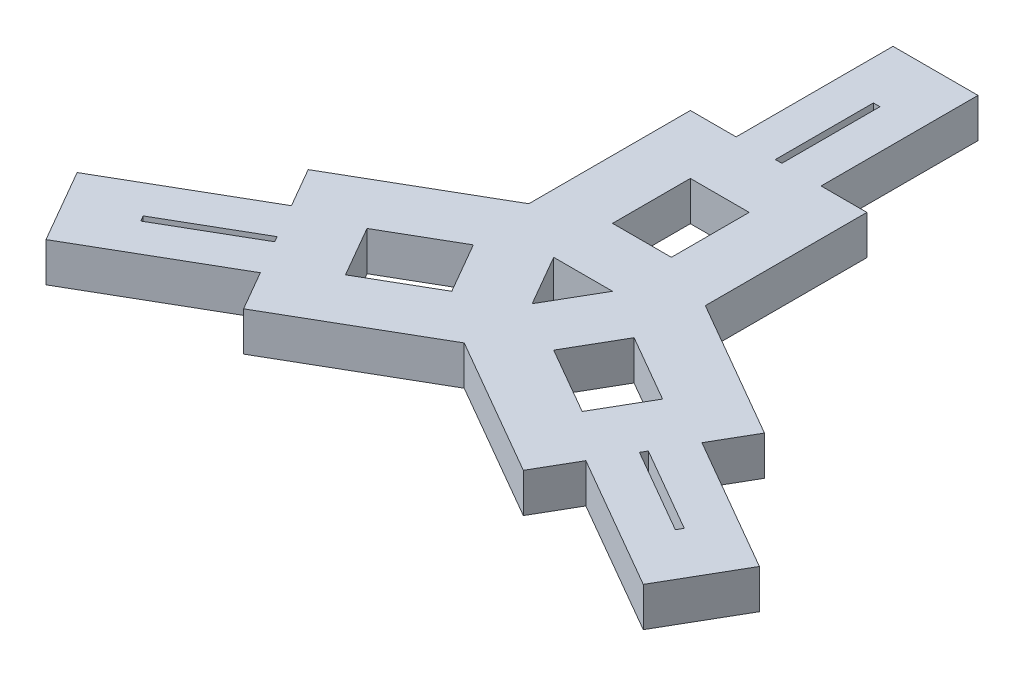
SolidWorks part; units mm, degrees
ref_plane "Alzado" through (0, 0, 0) normal (0, 0, 1) x (1, 0, 0)
ref_plane "Planta" through (0, 0, 0) normal (0, 1, 0) x (1, 0, 0)
ref_plane "Vista lateral" through (0, 0, 0) normal (1, 0, 0) x (0, 0, -1)
sketch "Croquis1" plane through (0, 0, 0) normal (0, 1, 0) x (1, 0, 0)
  line L0 (0, -1000) -> (0, 49000) construction
  line L1 (-1000, 0) -> (49000, 0) construction
  line L7 (-65, 475) -> (-5, 475)
  line L8 (-65, 475) -> (-65, 325)
  line L9 (-65, 325) -> (-5, 325)
  line L10 (-5, 475) -> (-5, 325)
  line L11 (-65, 475) -> (-5, 325) construction
  line L12 (-65, 325) -> (-5, 475) construction
  line L16 (65, 475) -> (5, 325) construction
  line L17 (65, 325) -> (5, 475) construction
  line L18 (65, 325) -> (5, 325)
  line L19 (5, 475) -> (5, 325)
  line L20 (65, 475) -> (5, 475)
  line L21 (65, 475) -> (65, 325)
  line L22 (-135, 235) -> (-135, 77.9423)
  line L23 (-65, 475) -> (65, 475)
  line L24 (-65, 475) -> (-65, 565)
  line L25 (-65, 565) -> (65, 565)
  line L26 (65, 475) -> (65, 565)
  line L35 (-135, 235) -> (135, 235)
  line L36 (-135, 235) -> (-135, 325)
  line L37 (-135, 325) -> (135, 325)
  line L38 (135, 235) -> (135, 325)
  line L39 (-135, 235) -> (135, 325) construction
  line L40 (-135, 325) -> (135, 235) construction
  line L41 (-45, 235) -> (-45, 25.9808)
  line L42 (45, 235) -> (45, 25.9808)
  line L43 (135, 235) -> (135, 77.9423)
  line L44 (378.8621, -293.7917) -> (278.9583, -166.8301) construction
  line L45 (248.9583, -218.7917) -> (408.8621, -241.8301) construction
  line L46 (313.9583, -106.2083) -> (413.8621, -233.1699) construction
  line L47 (443.8621, -181.2083) -> (283.9583, -158.1699) construction
  line L48 (443.8621, -181.2083) -> (313.9583, -106.2083)
  line L49 (443.8621, -181.2083) -> (413.8621, -233.1699)
  line L50 (413.8621, -233.1699) -> (283.9583, -158.1699)
  line L51 (313.9583, -106.2083) -> (283.9583, -158.1699)
  line L52 (248.9583, -218.7917) -> (278.9583, -166.8301)
  line L53 (408.8621, -241.8301) -> (278.9583, -166.8301)
  line L54 (378.8621, -293.7917) -> (408.8621, -241.8301)
  line L55 (378.8621, -293.7917) -> (248.9583, -218.7917)
  line L56 (443.8621, -181.2083) -> (521.8044, -226.2083)
  line L57 (443.8621, -181.2083) -> (378.8621, -293.7917)
  line L58 (378.8621, -293.7917) -> (456.8044, -338.7917)
  line L59 (521.8044, -226.2083) -> (456.8044, -338.7917)
  line L60 (271.016, -0.5866) -> (348.9583, -45.5866)
  line L61 (271.016, -0.5866) -> (136.016, -234.4134)
  line L62 (136.016, -234.4134) -> (213.9583, -279.4134)
  line L63 (348.9583, -45.5866) -> (213.9583, -279.4134)
  line L64 (226.016, -78.5289) -> (45, 25.9808)
  line L65 (271.016, -0.5866) -> (135, 77.9423)
  line L66 (181.016, -156.4711) -> (0, -51.9615)
  line L67 (136.016, -234.4134) -> (0, -155.8846)
  line L68 (-443.8621, -181.2083) -> (-283.9583, -158.1699) construction
  line L69 (-313.9583, -106.2083) -> (-413.8621, -233.1699) construction
  line L70 (-248.9583, -218.7917) -> (-408.8621, -241.8301) construction
  line L71 (-378.8621, -293.7917) -> (-278.9583, -166.8301) construction
  line L72 (-378.8621, -293.7917) -> (-248.9583, -218.7917)
  line L73 (-378.8621, -293.7917) -> (-408.8621, -241.8301)
  line L74 (-408.8621, -241.8301) -> (-278.9583, -166.8301)
  line L75 (-248.9583, -218.7917) -> (-278.9583, -166.8301)
  line L76 (-313.9583, -106.2083) -> (-283.9583, -158.1699)
  line L77 (-413.8621, -233.1699) -> (-283.9583, -158.1699)
  line L78 (-443.8621, -181.2083) -> (-413.8621, -233.1699)
  line L79 (-443.8621, -181.2083) -> (-313.9583, -106.2083)
  line L80 (-378.8621, -293.7917) -> (-456.8044, -338.7917)
  line L81 (-378.8621, -293.7917) -> (-443.8621, -181.2083)
  line L82 (-443.8621, -181.2083) -> (-521.8044, -226.2083)
  line L83 (-456.8044, -338.7917) -> (-521.8044, -226.2083)
  line L84 (-136.016, -234.4134) -> (-213.9583, -279.4134)
  line L85 (-136.016, -234.4134) -> (-271.016, -0.5866)
  line L86 (-271.016, -0.5866) -> (-348.9583, -45.5866)
  line L87 (-213.9583, -279.4134) -> (-348.9583, -45.5866)
  line L88 (-181.016, -156.4711) -> (0, -51.9615)
  line L89 (-136.016, -234.4134) -> (0, -155.8846)
  line L90 (-226.016, -78.5289) -> (-45, 25.9808)
  line L91 (-271.016, -0.5866) -> (-135, 77.9423)
  line L92 (-363.9102, -169.6891) -> (-328.9102, -230.3109) construction
  line L93 (363.9102, -169.6891) -> (328.9102, -230.3109)
  line L94 (-45, 25.9808) -> (0, -51.9615)
  line L95 (0, -51.9615) -> (45, 25.9808)
  line L96 (-45, 25.9808) -> (45, 25.9808)
  line L97 (-45, 115.9808) -> (45, 115.9808)
  line L98 (-122.9423, -19.0192) -> (-77.9423, -96.9615)
  line L99 (77.9423, -96.9615) -> (122.9423, -19.0192)
  line L100 (-45, 25.9808) -> (-135, 77.9423)
  circle A0 centre (0, 0) radius 400 construction
  point P3 (-35, 400)
  point P6 (0, 400)
  point P13 (0, 280)
  point P19 (35, 400)
  point P31 (363.9102, -169.6891)
  point P43 (328.9102, -230.3109)
  point P55 (-328.9102, -230.3109)
  point P65 (-363.9102, -169.6891)
  point P77 (0, 0)
  dimension "D1" = 800
  dimension "D2" = 60
  dimension "D3" = 150
  dimension "D4" = 70
  dimension "D5" = 90
  dimension "D6" = 90
  dimension "D7" = 270
  dimension "D8" = 90
  dimension "D12" = 130
  dimension "D13" = 270
  dimension "D14" = 209.0192
  dimension "D10" = 90
  dimension "D11" = 90
  dimension "D9" = 3
extrude "Saliente-Extruir1" add sketch "Croquis1" along normal blind 60
